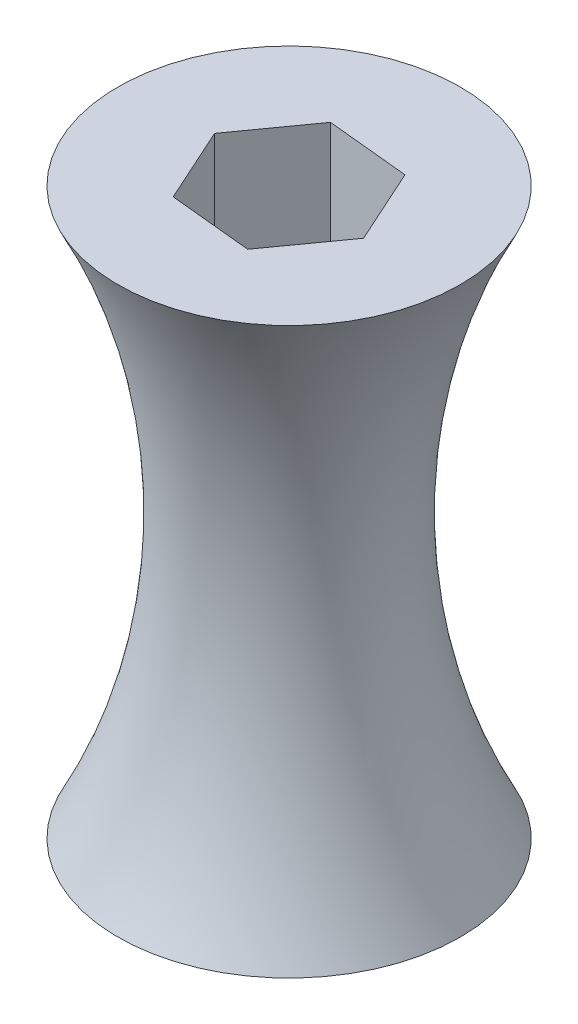
SolidWorks part; units mm, degrees
ref_plane "Front Plane" through (0, 0, 0) normal (0, 0, 1) x (1, 0, 0)
ref_plane "Top Plane" through (0, 0, 0) normal (0, 1, 0) x (1, 0, 0)
ref_plane "Right Plane" through (0, 0, 0) normal (1, 0, 0) x (0, 0, -1)
sketch "Sketch1" plane through (0, 0, 0) normal (0, 1, 0) x (1, 0, 0)
  circle A0 centre (0, 0) radius 19.05
extrude "Boss-Extrude1" add sketch "Sketch1" along normal blind 104.775
sketch "Sketch2" plane through (0, 0, 0) normal (0, -1, 0) x (1, 0, 0)
  line L1 (-15.3236, -1.5108) -> (-6.3534, -14.026)
  line L2 (-6.3534, -14.026) -> (8.9702, -12.5153)
  line L3 (8.9702, -12.5153) -> (15.3236, 1.5108)
  line L4 (15.3236, 1.5108) -> (6.3534, 14.026)
  line L5 (6.3534, 14.026) -> (-8.9702, 12.5153)
  line L6 (-8.9702, 12.5153) -> (-15.3236, -1.5108)
  circle A0 centre (0, 0) radius 13.335 construction
extrude "Cut-Extrude1" cut sketch "Sketch2" against normal up to surface (104.775 mm away) up to face at (0, 104.775, 19.05)
sketch "Sketch4" plane through (0, 0, 0) normal (0, 0, 1) x (1, 0, 0)
  line L0 (-19.05, 104.775) -> (-19.05, 0)
  line L1 (0, 0) -> (0, 104.775) construction
  line L2 (19.05, 104.775) -> (-19.05, 104.775) construction
  line L3 (-19.05, 104.775) -> (-31.75, 104.775)
  line L4 (-19.05, 0) -> (-31.75, 0)
  arc A2 (-31.75, 104.775) -> (-31.75, 0) centre (-133.4492, 52.3875) cw
  point P5 (-19.05, 104.775)
  point P13 (0, 0)
  point P14 (-19.05, 104.775)
  point P15 (0, 0)
  dimension "D1" = 12.7
revolve "Revolve3" add sketch "Sketch4" angle 360 about L1
